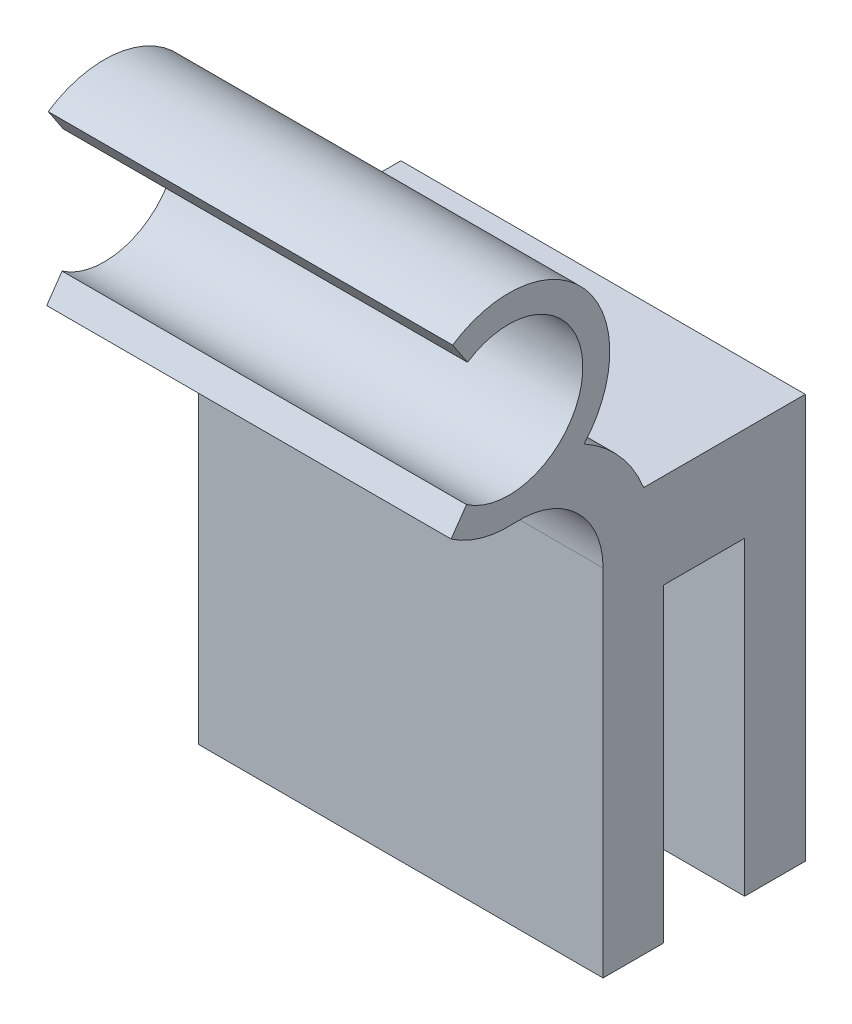
SolidWorks part; units mm, degrees
ref_plane "Alzado" through (0, 0, 0) normal (0, 0, 1) x (1, 0, 0)
ref_plane "Planta" through (0, 0, 0) normal (0, 1, 0) x (1, 0, 0)
ref_plane "Vista lateral" through (0, 0, 0) normal (1, 0, 0) x (0, 0, -1)
sketch "Croquis1" plane through (0, 0, 0) normal (1, 0, 0) x (0, 0, -1)
  line L0 (0, 55) -> (0, -55) construction
  line L1 (-4.4859, 10.5197) -> (7.5, 10.5197)
  line L2 (-7.5, 6.8622) -> (-7.5, -19.4803)
  line L3 (-7.5, -19.4803) -> (-3, -19.4803)
  line L4 (7.5, 10.5197) -> (7.5, -19.4803)
  line L6 (-3, -19.4803) -> (-3, 3.5197)
  line L7 (-3, 3.5197) -> (3, 3.5197)
  line L8 (3, -19.4803) -> (3, 3.5197)
  line L9 (3, -19.4803) -> (7.5, -19.4803)
  line L12 (-18.6591, 26.7608) -> (-17.55, 25.0965)
  line L13 (-18.7677, 14.3523) -> (-17.6296, 15.9969)
  arc A0 (-8.9022, 15.5282) -> (-18.6591, 26.7608) centre (-14.5, 20.5197) ccw
  arc A1 (-17.6296, 15.9969) -> (-17.55, 25.0965) centre (-14.5, 20.5197) ccw
  arc A3 (-7.5, 6.8622) -> (-14.0516, 13.0331) centre (-13.6819, 6.8622) ccw
  arc A4 (-4.4859, 10.5197) -> (-8.9022, 15.5282) centre (-13.6819, 6.8622) ccw
  arc A5 (-18.7677, 14.3523) -> (-14.0516, 13.0331) centre (-14.5, 20.5197) ccw
  dimension "D8" = 11
  dimension "D9" = 15
  dimension "D1" = 6
  dimension "D2" = 23
  dimension "D3" = 30
  dimension "D5" = 7.5
  dimension "D6" = 3
  dimension "D7" = 14.5
extrude "Saliente-Extruir1" add sketch "Croquis1" along normal mid plane 30
